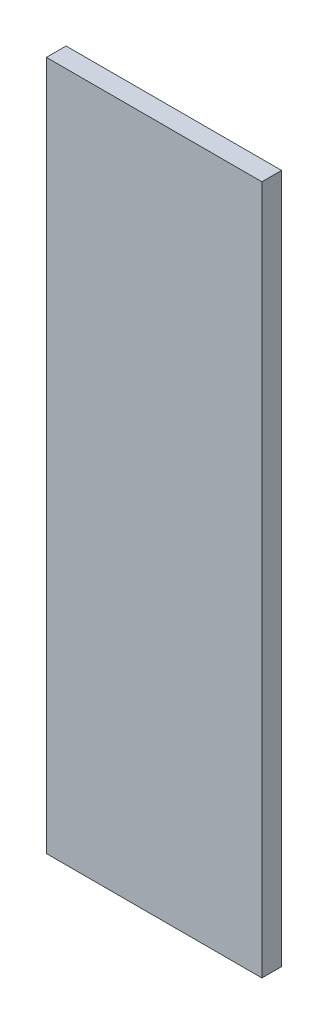
SolidWorks part; units mm, degrees
material "PVC Rigid"
ref_plane "Front" through (0, 0, 0) normal (0, 0, 1) x (1, 0, 0)
ref_plane "Top" through (0, 0, 0) normal (0, 1, 0) x (1, 0, 0)
ref_plane "Right" through (0, 0, 0) normal (1, 0, 0) x (0, 0, -1)
sketch "Sketch1" plane through (0, 0, 0) normal (0, 0, 1) x (1, 0, 0)
  line L5 (357.6645, 90.6213) -> (427.1645, 90.6213)
  line L6 (357.6645, 90.6213) -> (357.6645, -131.7787)
  line L7 (357.6645, -131.7787) -> (427.1645, -131.7787)
  line L8 (427.1645, 90.6213) -> (427.1645, -131.7787)
extrude "Boss-Extrude1" add sketch "Sketch1" against normal blind 6.35
